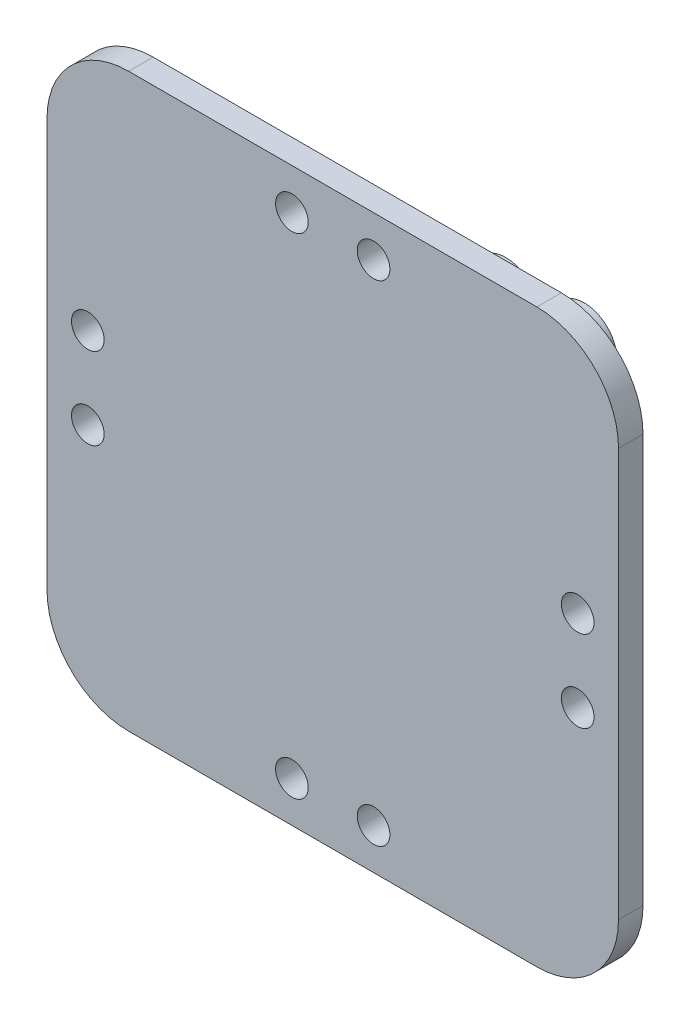
SolidWorks part; units mm, degrees
ref_plane "前视基准面" through (0, 0, 0) normal (0, 0, 1) x (1, 0, 0)
ref_plane "上视基准面" through (0, 0, 0) normal (0, 1, 0) x (1, 0, 0)
ref_plane "右视基准面" through (0, 0, 0) normal (1, 0, 0) x (0, 0, -1)
other "Configuration Table"
sketch "草图1" plane through (0, 0, 0) normal (0, 0, 1) x (1, 0, 0)
  line L1 (-18, -25) -> (18, -25)
  line L2 (-25, -18) -> (-25, 18)
  line L3 (-18, 25) -> (18, 25)
  line L4 (25, -18) -> (25, 18)
  line L5 (-25, -25) -> (25, 25) construction
  line L6 (-25, 25) -> (25, -25) construction
  circle A0 centre (20, 20) radius 1.75
  circle A1 centre (-20, 20) radius 1.75
  circle A2 centre (-20, -20) radius 1.75
  circle A3 centre (20, -20) radius 1.75
  arc A4 (18, -25) -> (25, -18) centre (18, -18) ccw
  arc A5 (-18, -25) -> (-25, -18) centre (-18, -18) cw
  arc A6 (18, 25) -> (25, 18) centre (18, 18) cw
  arc A7 (-25, 18) -> (-18, 25) centre (-18, 18) cw
  point P0 (0, 0)
  point P6 (20, 20)
  dimension "D3" = 5
  dimension "D6" = 3.5
  dimension "D7" = 3.5
  dimension "D4" = 3.5
  dimension "D8" = 3.5
  dimension "D11" = 7
  dimension "D1" = 50
  dimension "D2" = 50
  dimension "D5" = 5
  dimension "D9" = 5
  dimension "D10" = 5
extrude "凸台-拉伸3" add sketch "草图1" along normal blind 3 contours L2 A7 L3 A6 L4 A4 L1 A5 | A1 | A0 | A3 | A2
sketch "草图2" plane through (0, 0, 0) normal (0, 0, -1) x (-1, 0, 0)
  line L0 (18, 25) -> (-18, 25) construction
  line L1 (9.815, -17) -> (19.6299, 0)
  line L2 (19.6299, 0) -> (9.815, 17)
  line L3 (9.815, 17) -> (-9.815, 17)
  line L4 (-9.815, 17) -> (-19.6299, 0)
  line L5 (-19.6299, 0) -> (-9.815, -17)
  line L6 (-9.815, -17) -> (9.815, -17)
  circle A0 centre (0, 0) radius 17 construction
  dimension "D1" = 8
extrude "凸台-拉伸4" add sketch "草图2" along normal blind 15 contours L1 L2 L3 L4 L5 L6
sketch "草图3" plane through (0, 0, -15) normal (0, 0, -1) x (-1, 0, 0)
  line L2 (9.815, 17) -> (-9.815, 17) construction
  line L3 (0, 0) -> (-4.8151, 8.34) construction
  line L6 (-9.815, 17) -> (-19.6299, 0) construction
  line L7 (0, 0) -> (4.8151, 8.34) construction
  line L9 (19.6299, 0) -> (9.815, 17) construction
  circle A0 centre (-4.8151, 8.34) radius 1
  circle A6 centre (4.8151, 8.34) radius 1
  circle A8 centre (4.8151, -8.34) radius 1
  circle A9 centre (-4.8151, -8.34) radius 1
  circle A11 centre (-9.6302, 0) radius 1 [skipped]
  circle A12 centre (9.6302, 0) radius 1 [skipped]
  dimension "D3" = 2
  dimension "D6" = 2
  dimension "D7" = 8.66
  dimension "D2" = 8.66
  dimension "D4" = 6
  dimension "D1" = 8.66
  dimension "D5" = 60
  dimension "D8" = 8.66
extrude "切除-拉伸5" cut sketch "草图3" against normal blind 7.5
sketch "草图8" plane through (14.7224, 8.5, 0) normal (0.866, 0.5, 0) x (0, 0, -1)
  line L0 (15, 9.815) -> (15, -9.815) construction
  line L2 (15, 9.815) -> (0, 9.815) construction
  circle A0 centre (10, 4.815) radius 0.85
  dimension "D1" = 5
  dimension "D3" = 1.7
  dimension "D2" = 5
extrude "切除-拉伸8" cut sketch "草图8" against normal blind 9
sketch "草图10" plane through (-14.7224, 8.5, 0) normal (-0.866, 0.5, 0) x (0, 0, 1)
  line L0 (-15, 9.815) -> (0, 9.815) construction
  line L1 (-15, -9.815) -> (-15, 9.815) construction
  circle A0 centre (-10, 4.815) radius 0.85
  dimension "D1" = 5
  dimension "D3" = 1.7
  dimension "D2" = 5
extrude "切除-拉伸9" cut sketch "草图10" against normal blind 9
sketch "草图11" plane through (-14.7224, -8.5, 0) normal (-0.866, -0.5, 0) x (0, 0, 1)
  line L0 (-15, -9.815) -> (-15, 9.815) construction
  line L1 (-15, -9.815) -> (0, -9.815) construction
  circle A0 centre (-10, -4.815) radius 0.85
  dimension "D1" = 5
  dimension "D3" = 1.7
  dimension "D2" = 5
extrude "切除-拉伸10" cut sketch "草图11" against normal blind 9
sketch "草图12" plane through (14.7224, -8.5, 0) normal (0.866, -0.5, 0) x (0, 0, -1)
  line L0 (15, 9.815) -> (15, -9.815) construction
  line L1 (15, -9.815) -> (0, -9.815) construction
  circle A0 centre (10, -4.815) radius 0.85
  dimension "D1" = 5
  dimension "D3" = 1.7
  dimension "D2" = 5
extrude "切除-拉伸11" cut sketch "草图12" against normal blind 9
sketch "草图13" plane through (14.7224, 8.5, 0) normal (0.866, 0.5, 0) x (0, 0, -1)
  circle A0 centre (10, 4.815) radius 2
  circle A1 centre (10, 4.815) radius 0.85
  dimension "D1" = 4
  dimension "D2" = 1.7
extrude "凸台-拉伸5" add sketch "草图13" along normal blind 10
sketch "草图14" plane through (-14.7224, 8.5, 0) normal (-0.866, 0.5, 0) x (0, 0, 1)
  circle A0 centre (-10, 4.815) radius 2
  circle A1 centre (-10, 4.815) radius 0.85
  dimension "D1" = 4
  dimension "D2" = 1.7
extrude "凸台-拉伸6" add sketch "草图14" along normal blind 10
sketch "草图15" plane through (-14.7224, -8.5, 0) normal (-0.866, -0.5, 0) x (0, 0, 1)
  circle A0 centre (-10, -4.815) radius 2
  circle A1 centre (-10, -4.815) radius 0.85
  dimension "D1" = 4
  dimension "D2" = 1.7
extrude "凸台-拉伸7" add sketch "草图15" along normal blind 10
sketch "草图16" plane through (14.7224, -8.5, 0) normal (0.866, -0.5, 0) x (0, 0, -1)
  circle A0 centre (10, -4.815) radius 2
  circle A1 centre (10, -4.815) radius 0.85
  dimension "D1" = 4
  dimension "D2" = 1.7
extrude "凸台-拉伸8" add sketch "草图16" along normal blind 10
sketch "草图17" plane through (0, 0, -15) normal (0, 0, -1) x (-1, 0, 0)
  circle A0 centre (4.8151, 8.34) radius 4
  circle A1 centre (4.8151, 8.34) radius 2
  circle A2 centre (-4.8151, 8.34) radius 2
  circle A3 centre (-4.8151, 8.34) radius 4
  circle A4 centre (-4.8151, -8.34) radius 2
  circle A5 centre (-4.8151, -8.34) radius 4
  circle A6 centre (4.8151, -8.34) radius 2
  circle A7 centre (4.8151, -8.34) radius 4
  dimension "D1" = 8
  dimension "D2" = 4
  dimension "D3" = 8
  dimension "D4" = 4
  dimension "D5" = 8
  dimension "D6" = 4
  dimension "D7" = 8
  dimension "D8" = 4
extrude "凸台-拉伸9" add sketch "草图17" along normal blind 8
sketch "草图18" plane through (0, 0, 0) normal (0, 0, -1) x (-1, 0, 0)
  circle A0 centre (20, 20) radius 1.75
  circle A1 centre (-20, 20) radius 1.75
  circle A2 centre (-20, -20) radius 1.75
  circle A3 centre (20, -20) radius 1.75
extrude "凸台-拉伸10" add sketch "草图18" against normal blind 3
sketch "草图19" plane through (0, 0, 0) normal (0, 0, -1) x (-1, 0, 0)
  line L1 (-25, 35) -> (25, 35)
  line L2 (-35, 25) -> (-35, -25)
  line L3 (-25, -35) -> (25, -35)
  line L4 (35, 25) -> (35, -25)
  line L5 (-35, 35) -> (35, -35) construction
  line L6 (-35, -35) -> (35, 35) construction
  arc A0 (-35, -25) -> (-25, -35) centre (-25, -25) ccw
  arc A1 (-25, 35) -> (-35, 25) centre (-25, 25) ccw
  arc A2 (25, -35) -> (35, -25) centre (25, -25) ccw
  arc A3 (25, 35) -> (35, 25) centre (25, 25) cw
  circle A4 centre (-30, 5) radius 2
  circle A5 centre (-30, -5) radius 2
  circle A6 centre (-5, -30) radius 2
  circle A7 centre (5, -30) radius 2
  circle A8 centre (-5, 30) radius 2
  circle A9 centre (5, 30) radius 2
  circle A10 centre (30, 5) radius 2
  circle A11 centre (30, -5) radius 2
  point P0 (0, 0)
  dimension "D3" = 10
  dimension "D5" = 4
  dimension "D6" = 4
  dimension "D11" = 4
  dimension "D12" = 4
  dimension "D20" = 4
  dimension "D21" = 4
  dimension "D24" = 4
  dimension "D25" = 4
  dimension "D1" = 70
  dimension "D2" = 70
  dimension "D4" = 10
  dimension "D7" = 30
  dimension "D8" = 30
  dimension "D9" = 5
  dimension "D10" = 10
  dimension "D13" = 30
  dimension "D14" = 5
  dimension "D15" = 5
  dimension "D16" = 10
  dimension "D17" = 5
  dimension "D18" = 30
  dimension "D19" = 10
  dimension "D22" = 5
  dimension "D23" = 30
  dimension "D26" = 5
  dimension "D27" = 5
extrude "凸台-拉伸11" add sketch "草图19" against normal blind 3
